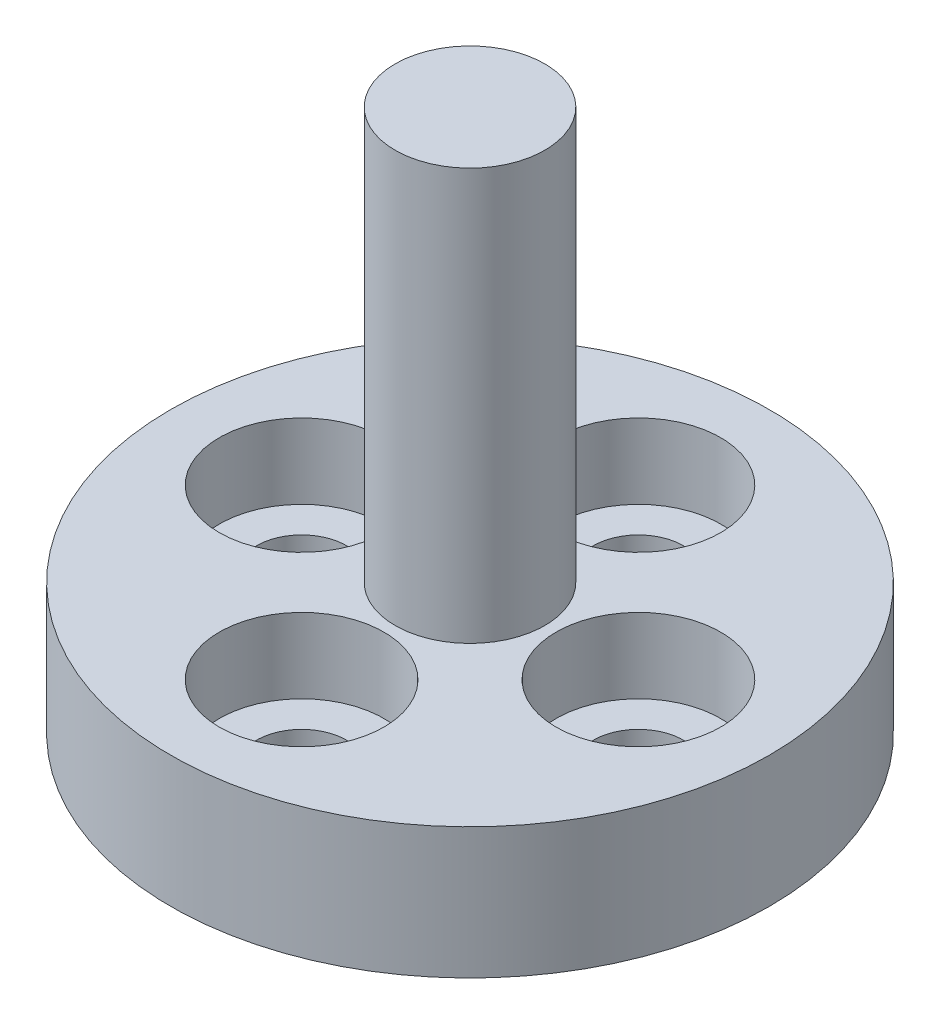
SolidWorks part; units mm, degrees
ref_plane "Front Plane" through (0, 0, 0) normal (0, 0, 1) x (1, 0, 0)
ref_plane "Top Plane" through (0, 0, 0) normal (0, 1, 0) x (1, 0, 0)
ref_plane "Right Plane" through (0, 0, 0) normal (1, 0, 0) x (0, 0, -1)
sketch "Sketch1" plane through (0, 0, 0) normal (0, 0, 1) x (1, 0, 0)
  line L0 (0, 0) -> (8, 0)
  line L1 (8, 0) -> (8, 3.5)
  line L2 (8, 3.5) -> (2, 3.5)
  line L3 (2, 3.5) -> (2, 14.5)
  line L4 (2, 14.5) -> (0, 14.5)
  line L5 (0, 14.5) -> (0, 0)
  dimension "D1" = 8
  dimension "D2" = 14.5
  dimension "D3" = 11
  dimension "D4" = 2
revolve "Revolve1" add sketch "Sketch1" angle 360 about L5
sketch "Sketch3" plane through (0, 3.5, 0) normal (0, 1, 0) x (1, 0, 0)
  circle A0 centre (0, 0) radius 4.5
  dimension "D1" = 9
hole_wizard "CBORE for M2 SHCS1" positions "Sketch6" profile "Sketch4" counterbore size "M2" standard "ANSI Metric" end condition through all
sketch "Sketch6" plane through (0, 3.5, 0) normal (0, 1, 0) x (1, 0, 0)
  circle A0 centre (0, 0) radius 4.5 construction
  point P0 (-4.5, 0)
  point P4 (0, 4.5)
  point P6 (4.5, 0)
  point P8 (0, -4.5)
sketch "Sketch4" plane through (-4.5, 3.5, 0) normal (1, 0, 0) x (0, 0, 1)
  line L0 (0, 0) -> (0, 3.5)
  line L1 (0, 3.5) -> (1.2, 3.5)
  line L3 (1.2, 3.5) -> (1.2, 2)
  line L4 (1.2, 2) -> (2.2, 2)
  line L5 (2.2, 2) -> (2.2, 0)
  line L7 (2.2, 0) -> (0, 0)
  line L11 (0, -6.35) -> (0, 107.95) construction
  dimension "Thru Hole Dia." = 2.4
  dimension "Thru Hole Depth" = 3.5
  dimension "C'Bore Dia." = 4.4
  dimension "C'Bore Depth" = 2
